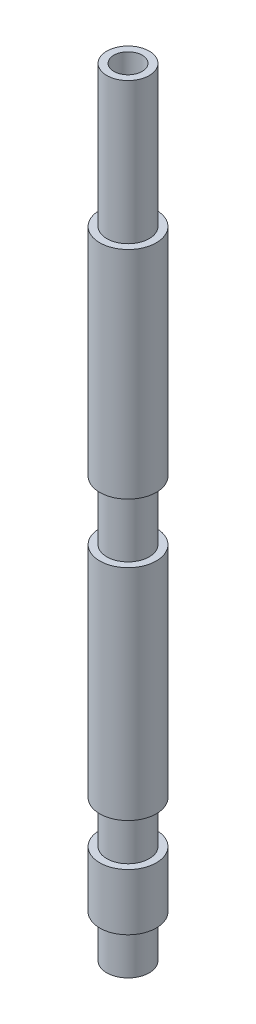
SolidWorks part; units mm, degrees
material "Простая углеродистая сталь"
ref_plane "Спереди" through (0, 0, 0) normal (0, 0, 1) x (1, 0, 0)
ref_plane "Сверху" through (0, 0, 0) normal (0, 1, 0) x (1, 0, 0)
ref_plane "Справа" through (0, 0, 0) normal (1, 0, 0) x (0, 0, -1)
sketch "Эскиз1" plane through (0, 0, 0) normal (0, 1, 0) x (1, 0, 0)
  circle A0 centre (0, 0) radius 2
  circle A1 centre (0, 0) radius 1
  dimension "D1" = 4
  dimension "D2" = 2
extrude "Бобышка-Вытянуть1" add sketch "Эскиз1" along normal blind 55
sketch "Эскиз2" plane through (0, 0, 0) normal (0, 0, 1) x (1, 0, 0)
  line L0 (1.5, 0) -> (2, 0)
  line L1 (1.5, 0) -> (1.5, 3)
  line L2 (2, 0) -> (2, 3)
  line L3 (1.5, 3) -> (2, 3)
  line L4 (0, 0) -> (0, 10.9491) construction
  line L5 (2, 7) -> (1.5, 7)
  line L6 (2, 7) -> (2, 10)
  line L7 (1.5, 7) -> (1.5, 10)
  line L8 (2, 10) -> (1.5, 10)
  line L10 (2, 0) -> (2, 55) construction
  line L11 (2, 55) -> (1.5, 55)
  line L12 (2, 55) -> (2, 45)
  line L13 (1.5, 55) -> (1.5, 45)
  line L14 (2, 45) -> (1.5, 45)
  line L15 (2, 55) -> (-2, 55) construction
  dimension "D1" = 0.5
  dimension "D2" = 3
  dimension "D3" = 3
  dimension "D4" = 0.5
  dimension "D5" = 7
  dimension "D6" = 0.5
  dimension "D7" = 10
revolve "Вырез-Повернуть1" cut sketch "Эскиз2" angle 360 about L4
sketch "Эскиз3" plane through (0, 0, 0) normal (0, 0, 1) x (1, 0, 0)
  line L0 (0, 0) -> (0, 20) construction
  dimension "D1" = 20
sketch "Эскиз4" plane through (0, 0, 0) normal (0, 0, 1) x (1, 0, 0)
  line L0 (-2, 25.5) -> (-1.5, 25.5)
  line L1 (-2, 25.5) -> (-2, 29.7)
  line L2 (-1.5, 25.5) -> (-1.5, 29.7)
  line L3 (-2, 29.7) -> (-1.5, 29.7)
  line L4 (-2, 45) -> (-2, 10) construction
  line L5 (-1.5, 0) -> (1.5, 0) construction
  dimension "D1" = 4.2
  dimension "D2" = 0.5
  dimension "D3" = 25.5
revolve "Вырез-Повернуть2" cut sketch "Эскиз4" angle 360 about L0
